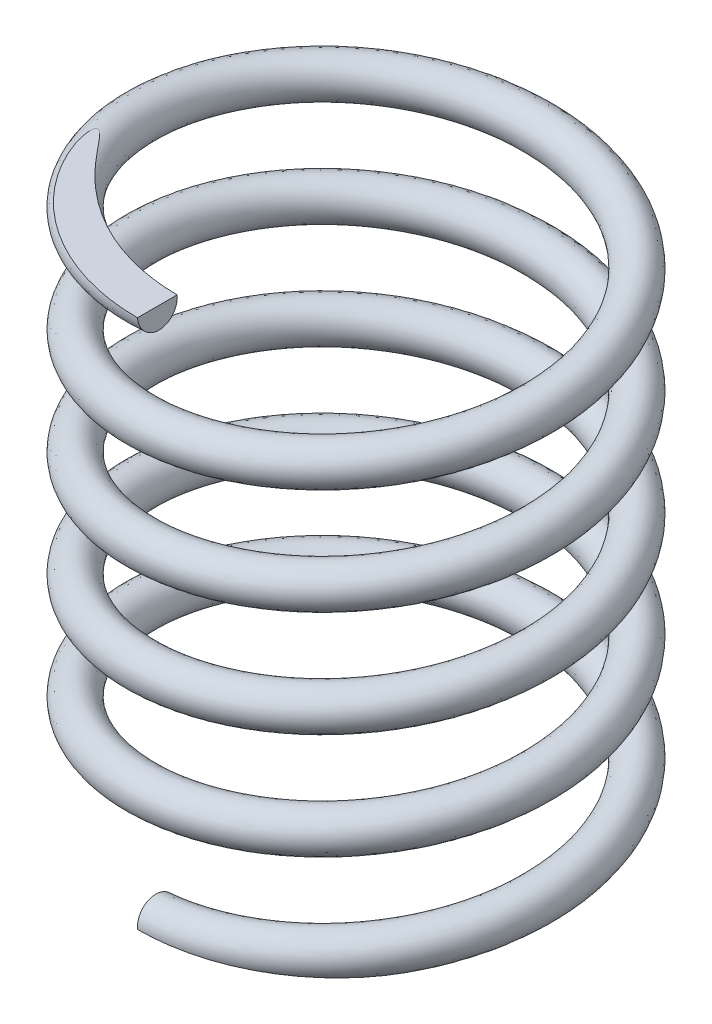
SolidWorks part; units mm, degrees
material "Пластичное железо (SN)"
ref_plane "Спереди" through (0, 0, 0) normal (0, 0, 1) x (1, 0, 0)
ref_plane "Сверху" through (0, 0, 0) normal (0, 1, 0) x (1, 0, 0)
ref_plane "Справа" through (0, 0, 0) normal (1, 0, 0) x (0, 0, -1)
sketch "Эскиз4" plane through (0, 0, 0) normal (0, 1, 0) x (1, 0, 0)
  circle A0 centre (0, 0) radius 7.5
  dimension "D1" = 15
curve "Спираль3" pitch 4 height 20 turns 5
ref_plane "Плоскость4" through (0, 0, 7.5) normal (0.9964, 0.0846, 0) x (0, 0, -1)
sketch "Эскиз5" plane through (0, 0, 7.5) normal (0.9964, 0.0846, 0) x (0, 0, -1)
  circle A0 centre (0, 0) radius 0.75
  point P1 (0, 0)
  point P3 (0, 0)
  dimension "D1" = 1.5
sweep "По траектории1" add profiles "Эскиз5" path "Спираль3"
ref_plane "Плоскость5" through (0, 0, 0) normal (0, 1, 0) x (1, 0, 0)
sketch "Эскиз6" plane through (0, 0, 0) normal (0, 1, 0) x (1, 0, 0)
  circle A0 centre (0, 0) radius 10.3377
  dimension "D1" = 20.6755
extrude "Вырез-Вытянуть1" cut sketch "Эскиз6" against normal blind 10
ref_plane "Плоскость6" through (0, 20, 0) normal (0, 1, 0) x (1, 0, 0)
sketch "Эскиз7" plane through (0, 20, 0) normal (0, 1, 0) x (1, 0, 0)
  circle A0 centre (0, 0) radius 10.1429
  dimension "D1" = 20.2859
extrude "Вырез-Вытянуть2" cut sketch "Эскиз7" along normal blind 10
